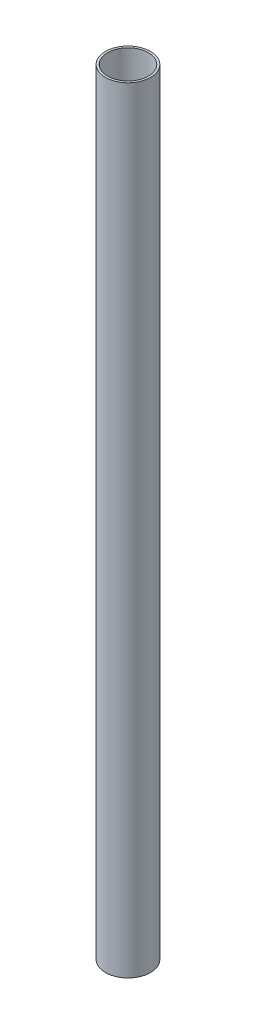
SolidWorks part; units mm, degrees
ref_plane "Front" through (0, 0, 0) normal (0, 0, 1) x (1, 0, 0)
ref_plane "Top" through (0, 0, 0) normal (0, 1, 0) x (1, 0, 0)
ref_plane "Right" through (0, 0, 0) normal (1, 0, 0) x (0, 0, -1)
sketch "Sketch1" plane through (0, 0, 0) normal (0, 1, 0) x (1, 0, 0)
  circle A0 centre (0, 0) radius 15.875
  circle A1 centre (0, 0) radius 14.351
  dimension "D1" = 31.75
  dimension "D2" = 28.702
extrude "Boss-Extrude1" add sketch "Sketch1" along normal blind 546.1 contours A1 | A0
